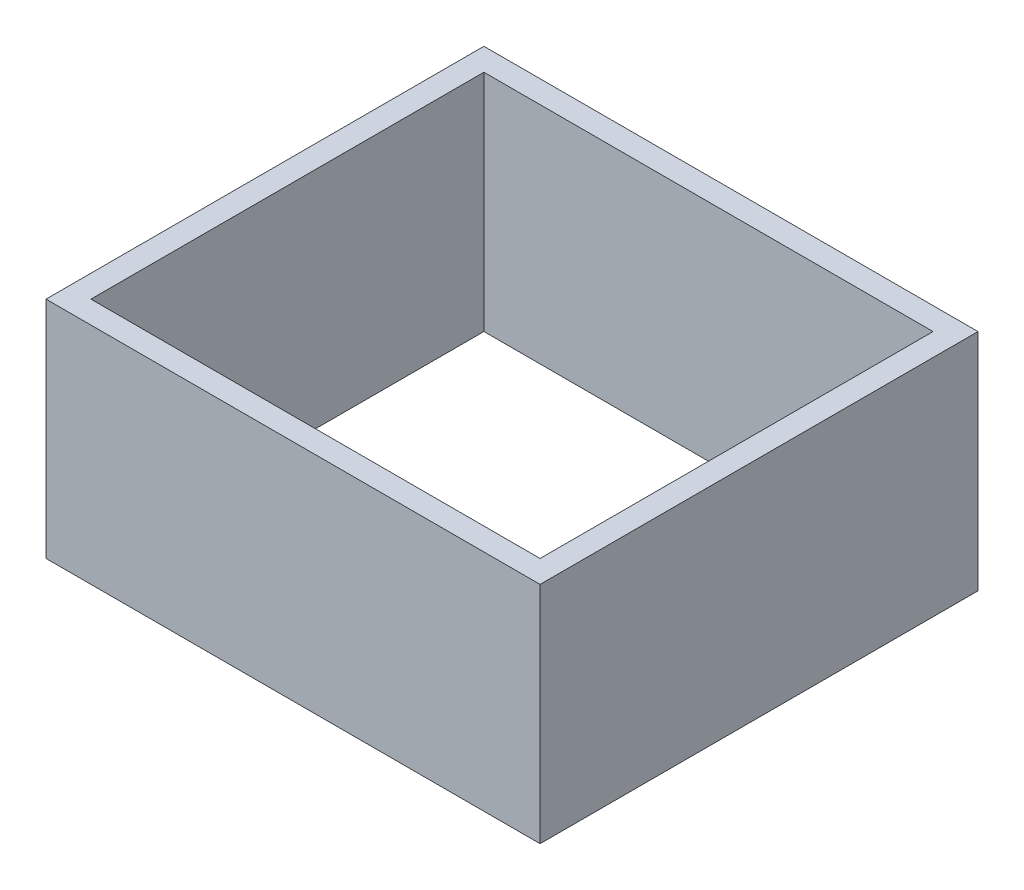
SolidWorks part; units mm, degrees
ref_plane "Front Plane" through (0, 0, 0) normal (0, 0, 1) x (1, 0, 0)
ref_plane "Top Plane" through (0, 0, 0) normal (0, 1, 0) x (1, 0, 0)
ref_plane "Right Plane" through (0, 0, 0) normal (1, 0, 0) x (0, 0, -1)
sketch "Sketch1" plane through (0, 0, 0) normal (0, 1, 0) x (1, 0, 0)
  line L0 (-30.9749, 35.6226) -> (24.9051, 35.6226)
  line L1 (24.9051, 35.6226) -> (24.9051, -13.9074)
  line L2 (24.9051, -13.9074) -> (-30.9749, -13.9074)
  line L3 (-30.9749, 35.6226) -> (-30.9749, -13.9074)
  point P4 (0, 0)
  dimension "D1" = 55.88
  dimension "D2" = 49.53
  dimension "D3" = 55.88
extrude "Boss-Extrude1" add sketch "Sketch1" along normal blind 25.4 contours L3 L2 L1 L0
sketch "Sketch2" plane through (0, 25.4, 0) normal (0, 1, 0) x (1, 0, 0)
  line L0 (-30.9749, 35.6226) -> (24.9051, 35.6226) construction
  line L1 (-28.4349, 33.0826) -> (22.3651, 33.0826)
  line L2 (-28.4349, 33.0826) -> (-28.4349, -11.3674)
  line L3 (-28.4349, -11.3674) -> (22.3651, -11.3674)
  line L4 (22.3651, 33.0826) -> (22.3651, -11.3674)
  line L5 (24.9051, -13.9074) -> (-30.9749, -13.9074) construction
  line L6 (24.9051, 35.6226) -> (24.9051, -13.9074) construction
  line L7 (-30.9749, 35.6226) -> (-30.9749, -13.9074) construction
  dimension "D1" = 2.54
  dimension "D2" = 2.54
  dimension "D3" = 2.54
  dimension "D4" = 2.54
extrude "Cut-Extrude1" cut sketch "Sketch2" against normal blind 25.4
